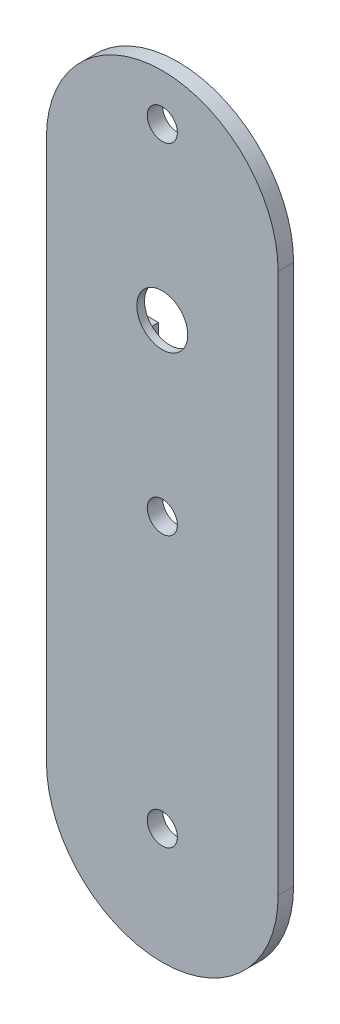
SolidWorks part; units mm, degrees
ref_plane "Plan de face" through (0, 0, 0) normal (0, 0, 1) x (1, 0, 0)
ref_plane "Plan de dessus" through (0, 0, 0) normal (0, 1, 0) x (1, 0, 0)
ref_plane "Plan de droite" through (0, 0, 0) normal (1, 0, 0) x (0, 0, -1)
sketch "Esquisse1" plane through (0, 0, 0) normal (0, 0, 1) x (1, 0, 0)
  line L0 (0, 0) -> (0, 70)
  line L1 (30, 70) -> (30, 0)
  line L2 (0, 0) -> (30, 0) construction
  line L3 (0, 70) -> (30, 70) construction
  line L4 (15, 70) -> (15, 0) construction
  arc A0 (0, 70) -> (30, 70) centre (15, 70) cw
  arc A1 (30, 0) -> (0, 0) centre (15, 0) cw
  dimension "D1" = 30
  dimension "D2" = 70
extrude "Boss.-Extru.1" add sketch "Esquisse1" along normal blind 2 contours A1 L1 A0 L0
sketch "Esquisse2" plane through (0, 0, 0) normal (0, 0, -1) x (-1, 0, 0)
  line L0 (-15, 85) -> (19.1023, 85) construction
  line L1 (-38.0047, 57) -> (22.5572, 57) construction
  line L2 (-15, 85) -> (-15, -26.094) construction
  line L3 (-72.0436, 79) -> (93.0914, 79) construction
  line L4 (-72.0436, 35) -> (93.0914, 35) construction
  arc A0 (0, 70) -> (-30, 70) centre (-15, 70) ccw construction
  dimension "D1" = 28
  dimension "D2" = 22
hole_wizard "Dégagement M3.51" positions "Esquisse4" profile "Esquisse3" hole size "M3.5" standard "Iso" end condition through all
sketch "Esquisse4" plane through (0, 0, 0) normal (0, 0, -1) x (-1, 0, 0)
  line L0 (-15, 85) -> (-15, -26.094) construction
  line L2 (-72.0436, 79) -> (93.0914, 79) construction
  line L3 (-72.0436, 35) -> (93.0914, 35) construction
  point P0 (-15, 79)
  point P8 (-15, 35)
sketch "Esquisse3" plane through (15, 79, 0) normal (1, 0, 0) x (0, 1, 0)
  line L0 (0, 0) -> (0, 2)
  line L1 (0, 2) -> (1.95, 2)
  line L2 (1.95, 2) -> (1.95, 0)
  line L5 (1.95, 0) -> (0, 0)
  line L11 (0, -6.35) -> (0, 107.95) construction
  dimension "Diamètre du perçage jusqu'au prochain" = 3.9
  dimension "Profondeur du perçage jusqu'au prochain" = 2
sketch "Esquisse5" plane through (0, 0, 0) normal (0, 0, -1) x (-1, 0, 0)
  line L0 (-12.5, 59.5) -> (-17.5, 54.5) construction
  line L1 (-17.5, 54.5) -> (-12.5, 54.5)
  line L2 (-17.5, 54.5) -> (-17.5, 59.5)
  line L3 (-17.5, 59.5) -> (-12.5, 59.5)
  line L4 (-12.5, 54.5) -> (-12.5, 59.5)
  line L5 (-17.5, 59.5) -> (-12.5, 54.5) construction
  line L6 (-15, 85) -> (-15, -26.094) construction
  line L7 (-38.0047, 57) -> (22.5572, 57) construction
  line L8 (-33.2846, 54.5) -> (1.9074, 54.5) construction
  line L9 (-12.5, 54.5) -> (-2.5, 54.5)
  line L10 (-12.5, 54.5) -> (-12.5, 59.5)
  line L11 (-12.5, 59.5) -> (-2.5, 59.5)
  line L12 (-2.5, 54.5) -> (-2.5, 59.5)
  line L13 (-33.8432, 59.5) -> (3.3225, 59.5) construction
  line L14 (-12.5, 54.5) -> (-12.5, 44.5)
  line L15 (-17.5, 44.5) -> (-12.5, 44.5)
  line L16 (-17.5, 54.5) -> (-17.5, 44.5)
  line L17 (-17.5, 54.5) -> (-27.5, 54.5)
  line L18 (-27.5, 59.5) -> (-27.5, 54.5)
  line L19 (-17.5, 59.5) -> (-27.5, 59.5)
  line L20 (-17.5, 59.5) -> (-17.5, 69.5)
  line L21 (-12.5, 69.5) -> (-17.5, 69.5)
  line L22 (-12.5, 59.5) -> (-12.5, 69.5)
  point P4 (-15, 57)
  point P32 (-15, 57)
  dimension "D1" = 5
  dimension "D2" = 5
  dimension "D3" = 10
  dimension "D4" = 4
extrude "Enlèv. mat.-Extru.3" cut sketch "Esquisse5" against normal blind 1
sketch "Esquisse7" plane through (0, 0, 0) normal (0, 0, -1) x (-1, 0, 0)
  line L0 (-69.7386, 0) -> (49.3, 0) construction
hole_wizard "Dégagement M3.52" positions "Esquisse9" profile "Esquisse8" hole size "M3.5" standard "Iso" end condition through all
sketch "Esquisse9" plane through (0, 0, 0) normal (0, 0, -1) x (-1, 0, 0)
  line L0 (-15, 85) -> (-15, -26.094) construction
  point P0 (-15, 0)
sketch "Esquisse8" plane through (15, 0, 0) normal (1, 0, 0) x (0, 1, 0)
  line L0 (0, 0) -> (0, 2)
  line L1 (0, 2) -> (1.95, 2)
  line L2 (1.95, 2) -> (1.95, 0)
  line L5 (1.95, 0) -> (0, 0)
  line L11 (0, -6.35) -> (0, 107.95) construction
  dimension "Diamètre du perçage jusqu'au prochain" = 3.9
  dimension "Profondeur du perçage jusqu'au prochain" = 2
hole_wizard "Dégagement M61" positions "Esquisse11" profile "Esquisse10" hole size "M6" standard "Iso" end condition through all
sketch "Esquisse11" plane through (0, 0, 0) normal (0, 0, -1) x (-1, 0, 0)
  line L0 (-38.0047, 57) -> (22.5572, 57) construction
  line L1 (-15, 85) -> (-15, -26.094) construction
  point P0 (-15, 57)
sketch "Esquisse10" plane through (15, 57, 0) normal (1, 0, 0) x (0, 1, 0)
  line L0 (0, 0) -> (0, 2)
  line L1 (0, 2) -> (3.3, 2)
  line L2 (3.3, 2) -> (3.3, 0)
  line L5 (3.3, 0) -> (0, 0)
  line L11 (0, -6.35) -> (0, 107.95) construction
  dimension "Diamètre du perçage jusqu'au prochain" = 6.6
  dimension "Profondeur du perçage jusqu'au prochain" = 2
